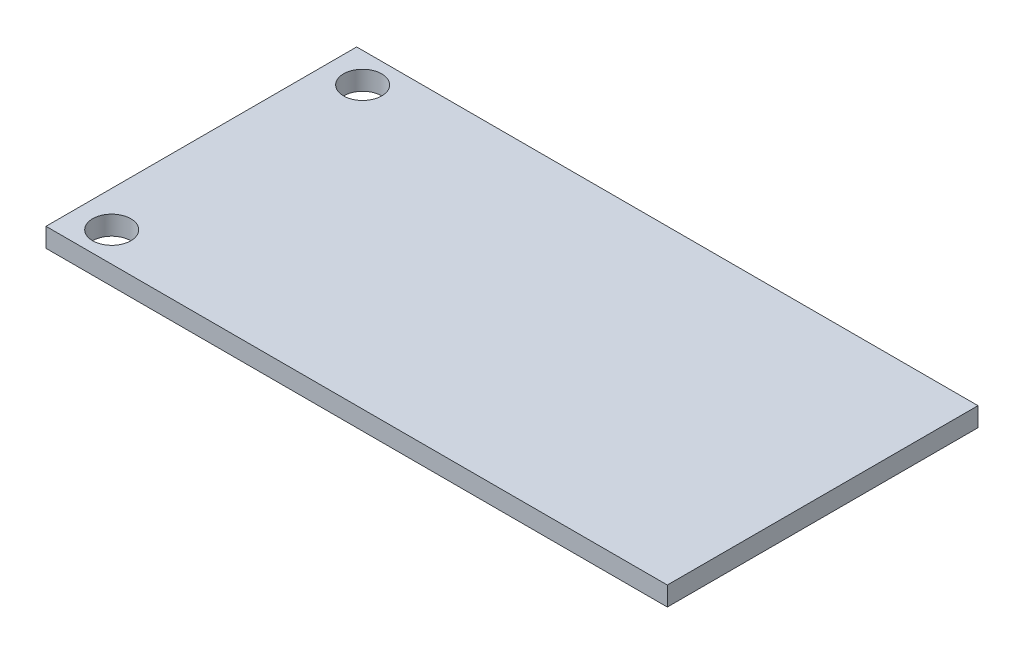
SolidWorks part; units mm, degrees
ref_plane "Front Plane" through (0, 0, 0) normal (0, 0, 1) x (1, 0, 0)
ref_plane "Top Plane" through (0, 0, 0) normal (0, 1, 0) x (1, 0, 0)
ref_plane "Right Plane" through (0, 0, 0) normal (1, 0, 0) x (0, 0, -1)
sketch "Sketch1" plane through (0, 0, 0) normal (0, 1, 0) x (1, 0, 0)
  line L1 (0, 0) -> (52, 0)
  line L2 (0, 0) -> (0, 26)
  line L3 (0, 26) -> (52, 26)
  line L4 (52, 0) -> (52, 26)
  circle A0 centre (3, 23.5) radius 1.6
  circle A1 centre (3, 2.5) radius 1.6
  dimension "D3" = 3.2
  dimension "D1" = 52
  dimension "D2" = 26
  dimension "D4" = 21
  dimension "D5" = 3
  dimension "D6" = 2.5
extrude "Boss-Extrude1" add sketch "Sketch1" along normal blind 1.6
